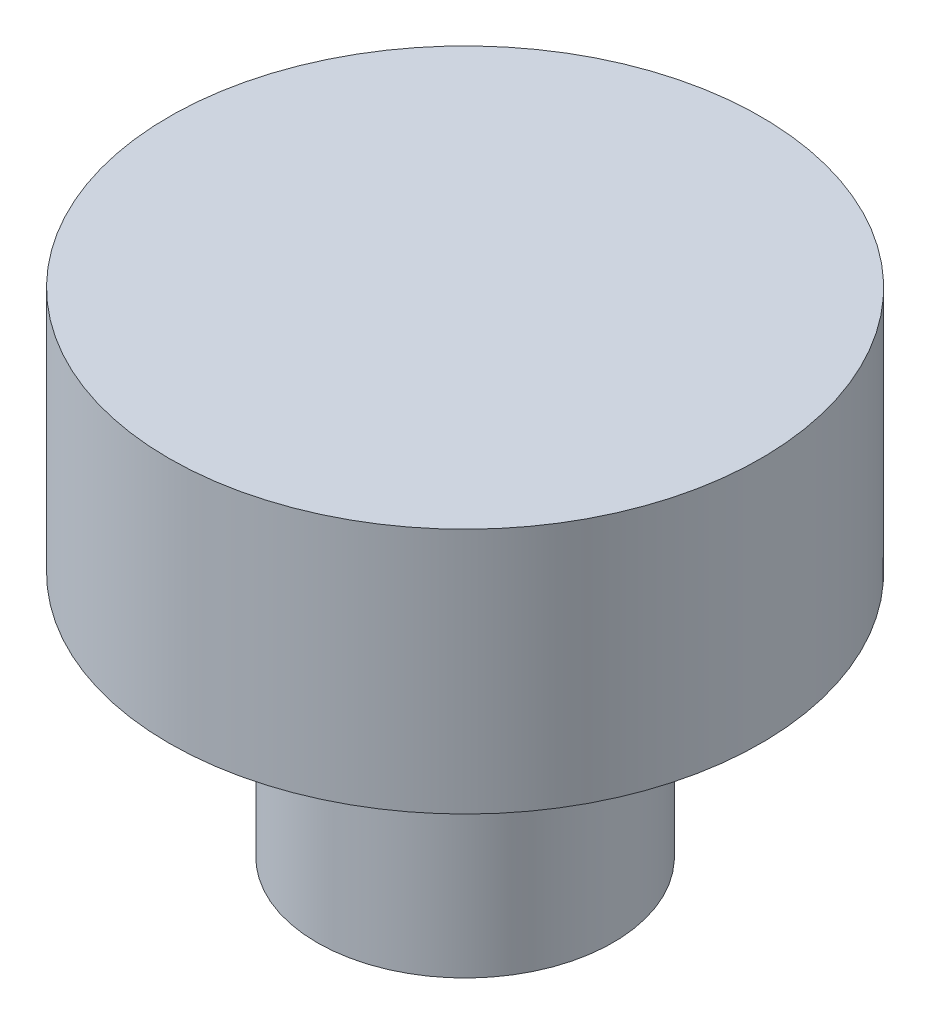
SolidWorks part; units mm, degrees
ref_plane "Спереди" through (0, 0, 0) normal (0, 0, 1) x (1, 0, 0)
ref_plane "Сверху" through (0, 0, 0) normal (0, 1, 0) x (1, 0, 0)
ref_plane "Справа" through (0, 0, 0) normal (1, 0, 0) x (0, 0, -1)
sketch "Эскиз1" plane through (0, 0, 0) normal (0, 1, 0) x (1, 0, 0)
  circle A0 centre (0, 0) radius 6
extrude "Бобышка-Вытянуть1" add sketch "Эскиз1" along normal blind 5
sketch "Эскиз2" plane through (0, 0, 0) normal (0, -1, 0) x (-1, 0, 0)
  circle A0 centre (0, 0) radius 3
extrude "Бобышка-Вытянуть2" add sketch "Эскиз2" along normal blind 5
sketch "Эскиз3" plane through (0, -5, 0) normal (0, -1, 0) x (-1, 0, 0)
  line L0 (0, 0) -> (3, 0)
  line L1 (3, 0) -> (-3, 0)
  line L2 (-3, 0) -> (0, -3)
  line L3 (0, -3) -> (0, 0)
  circle A0 centre (0, 0) radius 3 construction
